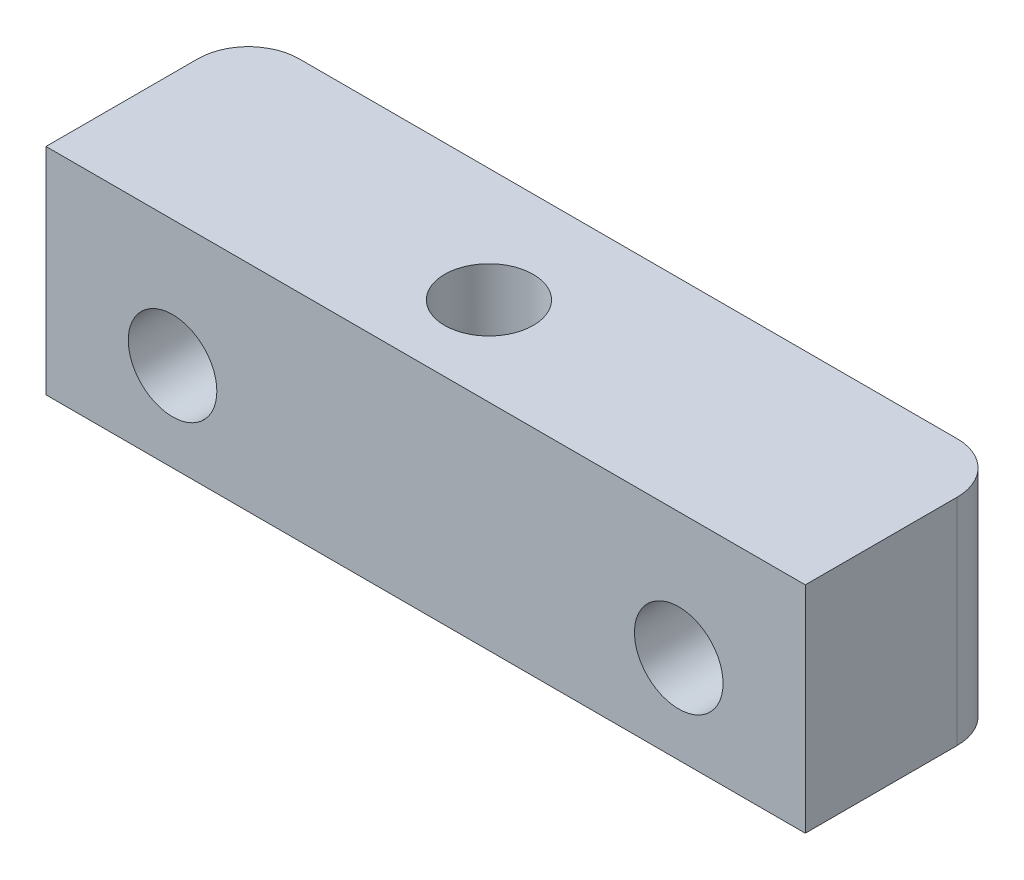
SolidWorks part; units mm, degrees
ref_plane "Front Plane" through (0, 0, 0) normal (0, 0, 1) x (1, 0, 0)
ref_plane "Top Plane" through (0, 0, 0) normal (0, 1, 0) x (1, 0, 0)
ref_plane "Right Plane" through (0, 0, 0) normal (1, 0, 0) x (0, 0, -1)
sketch "Sketch1" plane through (0, 0, 0) normal (0, 1, 0) x (1, 0, 0)
  line L0 (-1, -0.5) -> (-1, -4) construction
  line L5 (-15, 4) -> (15, 4)
  line L6 (-15, 4) -> (-15, -4)
  line L7 (-15, -4) -> (15, -4)
  line L8 (15, 4) -> (15, -4)
  line L9 (-15, 4) -> (15, -4) construction
  line L10 (-15, -4) -> (15, 4) construction
  line L11 (-1, 0) -> (0, 0) construction
  circle A0 centre (-1, -0.5) radius 1.75
  point P0 (0, 0)
  dimension "D3" = 3.5
  dimension "D1" = 30
  dimension "D2" = 8
  dimension "D4" = 3.5
  dimension "D5" = 1
extrude "Boss-Extrude1" add sketch "Sketch1" along normal blind 2
sketch "Sketch2" plane through (0, 0, 4) normal (0, 0, 1) x (1, 0, 0)
  line L0 (-10, -3) -> (10, -3) construction
  line L1 (-15, 0) -> (-5, 0)
  line L2 (-15, 0) -> (-15, -6.5)
  line L5 (15, 0) -> (5, 0)
  line L6 (15, 0) -> (15, -6.5)
  line L7 (15, -6.5) -> (-15, -6.5)
  line L10 (-15, 2) -> (15, 2) construction
  line L11 (-15, 0) -> (15, 0) construction
  line L23 (-5, 0) -> (5, 0)
  circle A2 centre (-10, -3) radius 1.75
  circle A3 centre (10, -3) radius 1.75
  point P5 (-14.6755, -6.5)
  point P12 (-10, 0)
  point P13 (10, 0)
  point P16 (-4.8639, -6.5)
  point P17 (0, -3)
  point P22 (0, 0)
  dimension "D1" = 3.5
  dimension "D2" = 3.5
  dimension "D3" = 5
  dimension "D4" = 6.5
  dimension "D5" = 20
extrude "Boss-Extrude2" add sketch "Sketch2" against normal up to surface (8 mm away) up to face at (0, 1, -4)
fillet "Fillet1" radius 2 2 edges at (-15, -2.25, -4) (15, -2.25, -4)
sketch "Sketch3" plane through (0, 0, 0) normal (0, 1, 0) x (1, 0, 0)
  circle A1 centre (-1, -0.5) radius 1.75
  circle A2 centre (-1, -0.5) radius 1.75
  dimension "D1" = 0
extrude "Cut-Extrude1" cut sketch "Sketch3" against normal through all
sketch "Sketch4" plane through (0, -6.5, 0) normal (0, -1, 0) x (1, 0, 0)
  line L1 (2.4641, 0.5) -> (0.7321, 3.5)
  line L2 (0.7321, 3.5) -> (-2.7321, 3.5)
  line L3 (-2.7321, 3.5) -> (-4.4641, 0.5)
  line L4 (-4.4641, 0.5) -> (-2.7321, -2.5)
  line L5 (-2.7321, -2.5) -> (0.7321, -2.5)
  line L6 (0.7321, -2.5) -> (2.4641, 0.5)
  circle A0 centre (-1, 0.5) radius 3 construction
  dimension "D1" = 6
extrude "Cut-Extrude2" cut sketch "Sketch4" against normal blind 3
